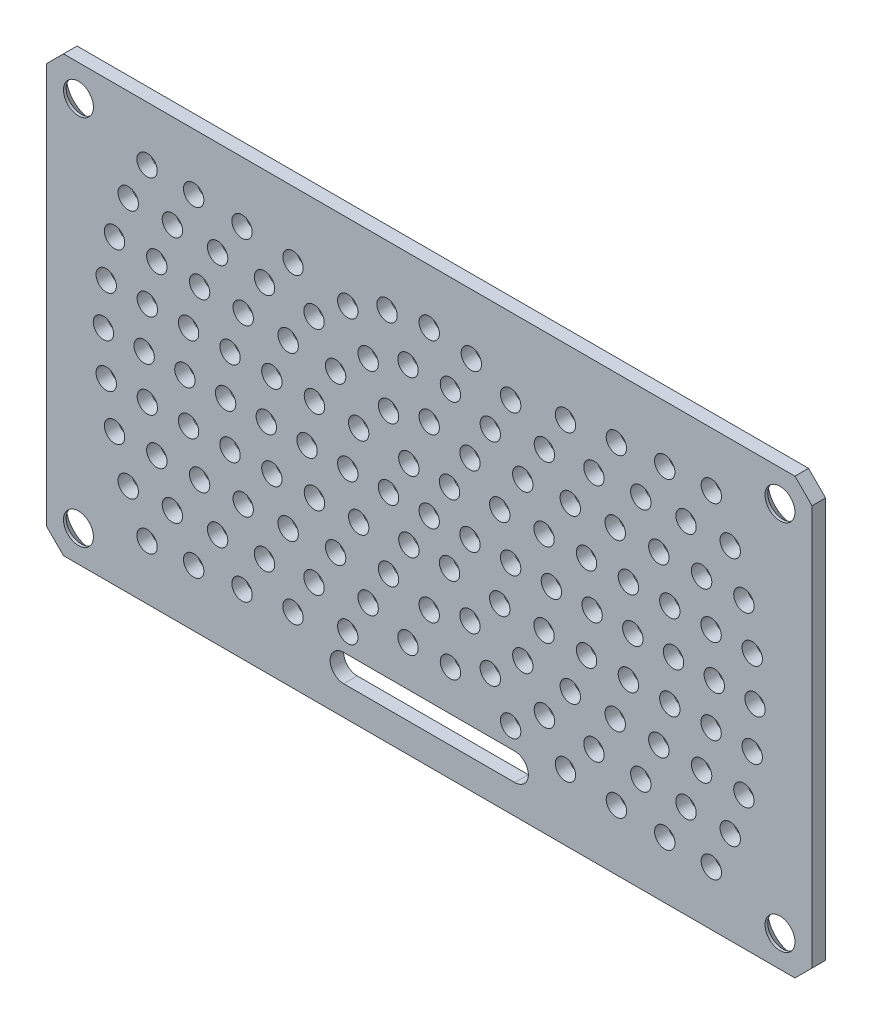
SolidWorks part; units mm, degrees
ref_plane "Front Plane" through (0, 0, 0) normal (0, 0, 1) x (1, 0, 0)
ref_plane "Top Plane" through (0, 0, 0) normal (0, 1, 0) x (1, 0, 0)
ref_plane "Right Plane" through (0, 0, 0) normal (1, 0, 0) x (0, 0, -1)
sketch "Sketch1" plane through (0, 0, 0) normal (0, 0, 1) x (1, 0, 0)
  line L1 (0, 0) -> (89.5, 0)
  line L2 (0, 0) -> (0, 50.8)
  line L3 (0, 50.8) -> (89.5, 50.8)
  line L4 (89.5, 0) -> (89.5, 50.8)
  dimension "D1" = 89.5
  dimension "D2" = 50.8
extrude "Boss-Extrude1" add sketch "Sketch1" along normal blind 1.5875
chamfer "Chamfer1" distance 2 angle 45 4 edges at (0, 0, 0.7937) (0, 50.8, 0.7937) (89.5, 0, 0.7937) (89.5, 50.8, 0.7937)
sketch "Sketch3" plane through (0, 0, 0) normal (0, 0, -1) x (-1, 0, 0)
  line L0 (-89.5, 25.4) -> (0, 25.4) construction
  line L1 (-89.5, 2) -> (-89.5, 48.8) construction
  line L2 (0, 48.8) -> (0, 2) construction
  line L3 (-85.75, 47.15) -> (-3.75, 47.15) construction
  line L4 (-87.5, 50.8) -> (-2, 50.8) construction
  line L5 (-44.75, 50.8) -> (-44.75, 0) construction
  line L6 (-2, 0) -> (-87.5, 0) construction
  line L7 (-3.75, 47.15) -> (-3.75, 3.65) construction
  circle A0 centre (-85.75, 47.15) radius 1.75
  circle A1 centre (-3.75, 47.15) radius 1.75
  circle A2 centre (-3.75, 3.65) radius 1.75
  circle A3 centre (-85.75, 3.65) radius 1.75
  point P20 (-44.75, 47.15)
  point P21 (-3.75, 25.4)
  dimension "D1" = 3.5
  dimension "D2" = 82
  dimension "D3" = 43.5
extrude "Cut-Extrude2" cut sketch "Sketch3" against normal through all
chamfer "Chamfer2" distance 1.27 angle 45 4 edges at (2, 3.65, 0) (84, 3.65, 0) (2, 47.15, 0) (84, 47.15, 0)
sketch "Sketch4" plane through (0, 0, 0) normal (0, 0, -1) x (-1, 0, 0)
  line L0 (-44.75, 50.8) -> (-44.75, 0) construction
  line L1 (-87.5, 50.8) -> (-2, 50.8) construction
  line L2 (-2, 0) -> (-87.5, 0) construction
  circle A0 centre (-44.75, 25.4) radius 1.1906
  circle A1 centre (-39.99, 25.4) radius 1.1906
  circle A2 centre (-35.23, 25.4) radius 1.1906
  circle A3 centre (-30.47, 25.4) radius 1.1906
  circle A4 centre (-25.71, 25.4) radius 1.1906
  circle A5 centre (-20.95, 25.4) radius 1.1906
  circle A6 centre (-16.19, 25.4) radius 1.1906
  circle A7 centre (-11.43, 25.4) radius 1.1906
  circle A8 centre (-6.67, 25.4) radius 1.1906
  circle A10 centre (-42.37, 21.2777) radius 1.1906
  circle A11 centre (-47.13, 21.2777) radius 1.1906
  circle A12 centre (-49.51, 25.4) radius 1.1906
  circle A13 centre (-47.13, 29.5223) radius 1.1906
  circle A14 centre (-42.37, 29.5223) radius 1.1906
  circle A15 centre (-36.5054, 20.64) radius 1.1906
  circle A16 centre (-39.99, 17.1554) radius 1.1906
  circle A17 centre (-44.75, 15.88) radius 1.1906
  circle A18 centre (-49.51, 17.1554) radius 1.1906
  circle A19 centre (-52.9946, 20.64) radius 1.1906
  circle A20 centre (-54.27, 25.4) radius 1.1906
  circle A21 centre (-52.9946, 30.16) radius 1.1906
  circle A22 centre (-49.51, 33.6446) radius 1.1906
  circle A23 centre (-44.75, 34.92) radius 1.1906
  circle A24 centre (-39.99, 33.6446) radius 1.1906
  circle A25 centre (-36.5054, 30.16) radius 1.1906
  circle A26 centre (-31.3312, 20.516) radius 1.1906
  circle A27 centre (-33.8109, 16.221) radius 1.1906
  circle A28 centre (-37.61, 13.0332) radius 1.1906
  circle A29 centre (-42.2703, 11.3369) radius 1.1906
  circle A30 centre (-47.2297, 11.3369) radius 1.1906
  circle A31 centre (-51.89, 13.0332) radius 1.1906
  circle A32 centre (-55.6891, 16.221) radius 1.1906
  circle A33 centre (-58.1688, 20.516) radius 1.1906
  circle A34 centre (-59.03, 25.4) radius 1.1906
  circle A35 centre (-58.1688, 30.284) radius 1.1906
  circle A36 centre (-55.6891, 34.579) radius 1.1906
  circle A37 centre (-51.89, 37.7668) radius 1.1906
  circle A38 centre (-47.2297, 39.4631) radius 1.1906
  circle A39 centre (-42.2703, 39.4631) radius 1.1906
  circle A40 centre (-37.61, 37.7668) radius 1.1906
  circle A41 centre (-33.8109, 34.579) radius 1.1906
  circle A42 centre (-31.3312, 30.284) radius 1.1906
  circle A43 centre (-26.3588, 20.4721) radius 1.1906
  circle A44 centre (-28.2609, 15.88) radius 1.1906
  circle A45 centre (-31.2867, 11.9367) radius 1.1906
  circle A46 centre (-35.23, 8.9109) radius 1.1906
  circle A50 centre (-54.27, 8.9109) radius 1.1906
  circle A51 centre (-58.2133, 11.9367) radius 1.1906
  circle A52 centre (-61.2391, 15.88) radius 1.1906
  circle A53 centre (-63.1412, 20.4721) radius 1.1906
  circle A54 centre (-63.79, 25.4) radius 1.1906
  circle A55 centre (-63.1412, 30.3279) radius 1.1906
  circle A56 centre (-61.2391, 34.92) radius 1.1906
  circle A57 centre (-58.2133, 38.8633) radius 1.1906
  circle A58 centre (-54.27, 41.8891) radius 1.1906
  circle A59 centre (-49.6779, 43.7912) radius 1.1906
  circle A60 centre (-44.75, 44.44) radius 1.1906
  circle A61 centre (-39.8221, 43.7912) radius 1.1906
  circle A62 centre (-35.23, 41.8891) radius 1.1906
  circle A63 centre (-31.2867, 38.8633) radius 1.1906
  circle A64 centre (-28.2609, 34.92) radius 1.1906
  circle A65 centre (-26.3588, 30.3279) radius 1.1906
  circle A66 centre (-21.4701, 20.4517) radius 1.1906
  circle A67 centre (-23.0076, 15.7197) radius 1.1906
  circle A68 centre (-25.4954, 11.4107) radius 1.1906
  circle A69 centre (-28.8247, 7.7132) radius 1.1906
  circle A76 centre (-60.6753, 7.7132) radius 1.1906
  circle A77 centre (-64.0046, 11.4107) radius 1.1906
  circle A78 centre (-66.4924, 15.7197) radius 1.1906
  circle A79 centre (-68.0299, 20.4517) radius 1.1906
  circle A80 centre (-68.55, 25.4) radius 1.1906
  circle A81 centre (-68.0299, 30.3483) radius 1.1906
  circle A82 centre (-66.4924, 35.0803) radius 1.1906
  circle A83 centre (-64.0046, 39.3893) radius 1.1906
  circle A84 centre (-60.6753, 43.0868) radius 1.1906
  circle A91 centre (-28.8247, 43.0868) radius 1.1906
  circle A92 centre (-25.4954, 39.3893) radius 1.1906
  circle A93 centre (-23.0076, 35.0803) radius 1.1906
  circle A94 centre (-21.4701, 30.3483) radius 1.1906
  circle A95 centre (-16.6239, 20.4406) radius 1.1906
  circle A96 centre (-17.9124, 15.6319) radius 1.1906
  circle A97 centre (-20.0163, 11.12) radius 1.1906
  circle A98 centre (-22.8718, 7.042) radius 1.1906
  circle A108 centre (-66.6282, 7.042) radius 1.1906
  circle A109 centre (-69.4837, 11.12) radius 1.1906
  circle A110 centre (-71.5876, 15.6319) radius 1.1906
  circle A111 centre (-72.8761, 20.4406) radius 1.1906
  circle A112 centre (-73.31, 25.4) radius 1.1906
  circle A113 centre (-72.8761, 30.3594) radius 1.1906
  circle A114 centre (-71.5876, 35.1681) radius 1.1906
  circle A115 centre (-69.4837, 39.68) radius 1.1906
  circle A116 centre (-66.6282, 43.758) radius 1.1906
  circle A126 centre (-22.8718, 43.758) radius 1.1906
  circle A127 centre (-20.0163, 39.68) radius 1.1906
  circle A128 centre (-17.9124, 35.1681) radius 1.1906
  circle A129 centre (-16.6239, 30.3594) radius 1.1906
  circle A130 centre (-11.8022, 20.4339) radius 1.1906
  circle A131 centre (-12.9103, 15.5788) radius 1.1906
  circle A132 centre (-14.7297, 10.943) radius 1.1906
  circle A133 centre (-17.2197, 6.6302) radius 1.1906
  circle A146 centre (-72.2803, 6.6302) radius 1.1906
  circle A147 centre (-74.7703, 10.943) radius 1.1906
  circle A148 centre (-76.5897, 15.5788) radius 1.1906
  circle A149 centre (-77.6978, 20.4339) radius 1.1906
  circle A150 centre (-78.07, 25.4) radius 1.1906
  circle A151 centre (-77.6978, 30.3661) radius 1.1906
  circle A152 centre (-76.5897, 35.2212) radius 1.1906
  circle A153 centre (-74.7703, 39.857) radius 1.1906
  circle A154 centre (-72.2803, 44.1698) radius 1.1906
  circle A167 centre (-17.2197, 44.1698) radius 1.1906
  circle A168 centre (-14.7297, 39.857) radius 1.1906
  circle A169 centre (-12.9103, 35.2212) radius 1.1906
  circle A170 centre (-11.8022, 30.3661) radius 1.1906
  circle A171 centre (-6.9958, 20.4296) radius 1.1906
  circle A172 centre (-7.9675, 15.5442) radius 1.1906
  circle A173 centre (-9.5687, 10.8274) radius 1.1906
  circle A174 centre (-11.7718, 6.36) radius 1.1906
  circle A190 centre (-77.7282, 6.36) radius 1.1906
  circle A191 centre (-79.9313, 10.8274) radius 1.1906
  circle A192 centre (-81.5325, 15.5442) radius 1.1906
  circle A193 centre (-82.5042, 20.4296) radius 1.1906
  circle A194 centre (-82.83, 25.4) radius 1.1906
  circle A195 centre (-82.5042, 30.3704) radius 1.1906
  circle A196 centre (-81.5325, 35.2558) radius 1.1906
  circle A197 centre (-79.9313, 39.9726) radius 1.1906
  circle A198 centre (-77.7282, 44.44) radius 1.1906
  circle A214 centre (-11.7718, 44.44) radius 1.1906
  circle A215 centre (-9.5687, 39.9726) radius 1.1906
  circle A216 centre (-7.9675, 35.2558) radius 1.1906
  circle A217 centre (-6.9958, 30.3704) radius 1.1906
  circle A271 centre (-49.7094, 53.5261) radius 1.1906 [skipped]
  circle A272 centre (-44.75, 53.96) radius 1.1906 [skipped]
  circle A273 centre (-39.7906, 53.5261) radius 1.1906 [skipped]
  circle A274 centre (-61.41, 54.256) radius 1.1906 [skipped]
  circle A275 centre (-56.9232, 56.4167) radius 1.1906 [skipped]
  circle A276 centre (-52.1644, 57.8846) radius 1.1906 [skipped]
  circle A277 centre (-47.24, 58.6268) radius 1.1906 [skipped]
  circle A278 centre (-42.26, 58.6268) radius 1.1906 [skipped]
  circle A279 centre (-37.3356, 57.8846) radius 1.1906 [skipped]
  circle A280 centre (-32.5768, 56.4167) radius 1.1906 [skipped]
  circle A281 centre (-28.09, 54.256) radius 1.1906 [skipped]
  circle A282 centre (-71.6766, 52.3266) radius 1.1906 [skipped]
  circle A283 centre (-67.9316, 55.6109) radius 1.1906 [skipped]
  circle A284 centre (-63.79, 58.3782) radius 1.1906 [skipped]
  circle A285 centre (-59.3226, 60.5813) radius 1.1906 [skipped]
  circle A286 centre (-54.6058, 62.1825) radius 1.1906 [skipped]
  circle A287 centre (-49.7204, 63.1542) radius 1.1906 [skipped]
  circle A288 centre (-44.75, 63.48) radius 1.1906 [skipped]
  circle A289 centre (-39.7796, 63.1542) radius 1.1906 [skipped]
  circle A290 centre (-34.8942, 62.1825) radius 1.1906 [skipped]
  circle A291 centre (-30.1774, 60.5813) radius 1.1906 [skipped]
  circle A292 centre (-25.71, 58.3782) radius 1.1906 [skipped]
  circle A293 centre (-21.5684, 55.6109) radius 1.1906 [skipped]
  circle A309 centre (-59.03, 50.1337) radius 1.1906 [skipped]
  circle A310 centre (-54.5181, 52.2376) radius 1.1906 [skipped]
  circle A311 centre (-65.5247, 51.4506) radius 1.1906 [skipped]
  circle A312 centre (-23.9753, 51.4506) radius 1.1906 [skipped]
  circle A313 centre (-17.8234, 52.3266) radius 1.1906 [skipped]
  circle A315 centre (-34.9819, 52.2376) radius 1.1906 [skipped]
  circle A316 centre (-30.47, 50.1337) radius 1.1906 [skipped]
  circle A319 centre (-34.9819, -1.4376) radius 1.1906 [skipped]
  circle A320 centre (-39.7906, -2.7261) radius 1.1906 [skipped]
  circle A321 centre (-44.75, -3.16) radius 1.1906 [skipped]
  circle A322 centre (-49.7094, -2.7261) radius 1.1906 [skipped]
  circle A323 centre (-54.5181, -1.4376) radius 1.1906 [skipped]
  circle A324 centre (-23.9753, -0.6506) radius 1.1906 [skipped]
  circle A325 centre (-28.09, -3.456) radius 1.1906 [skipped]
  circle A326 centre (-32.5768, -5.6167) radius 1.1906 [skipped]
  circle A327 centre (-37.3356, -7.0846) radius 1.1906 [skipped]
  circle A328 centre (-42.26, -7.8268) radius 1.1906 [skipped]
  circle A329 centre (-47.24, -7.8268) radius 1.1906 [skipped]
  circle A330 centre (-52.1644, -7.0846) radius 1.1906 [skipped]
  circle A331 centre (-56.9232, -5.6167) radius 1.1906 [skipped]
  circle A332 centre (-61.41, -3.456) radius 1.1906 [skipped]
  circle A333 centre (-65.5247, -0.6506) radius 1.1906 [skipped]
  circle A334 centre (-17.8234, -1.5266) radius 1.1906 [skipped]
  circle A335 centre (-21.5684, -4.8109) radius 1.1906 [skipped]
  circle A336 centre (-25.71, -7.5782) radius 1.1906 [skipped]
  circle A337 centre (-30.1774, -9.7813) radius 1.1906 [skipped]
  circle A338 centre (-34.8942, -11.3825) radius 1.1906 [skipped]
  circle A339 centre (-39.7796, -12.3542) radius 1.1906 [skipped]
  circle A340 centre (-44.75, -12.68) radius 1.1906 [skipped]
  circle A341 centre (-49.7204, -12.3542) radius 1.1906 [skipped]
  circle A342 centre (-54.6058, -11.3825) radius 1.1906 [skipped]
  circle A343 centre (-59.3226, -9.7813) radius 1.1906 [skipped]
  circle A344 centre (-63.79, -7.5782) radius 1.1906 [skipped]
  circle A345 centre (-67.9316, -4.8109) radius 1.1906 [skipped]
  circle A346 centre (-71.6766, -1.5266) radius 1.1906 [skipped]
  circle A363 centre (-59.03, 0.6663) radius 1.1906 [skipped]
  circle A364 centre (-30.47, 0.6663) radius 1.1906 [skipped]
  circle A367 centre (-42.2622, 1.7304) radius 1.1906 [skipped]
  circle A368 centre (-47.2378, 1.7304) radius 1.1906 [skipped]
  circle A369 centre (-47.2378, 49.0696) radius 1.1906 [skipped]
  circle A370 centre (-42.2622, 49.0696) radius 1.1906 [skipped]
  circle A371 centre (-52.1046, 48.0351) radius 1.1906 [skipped]
  circle A372 centre (-37.3954, 48.0351) radius 1.1906 [skipped]
  circle A373 centre (-37.3954, 2.7649) radius 1.1906 [skipped]
  circle A374 centre (-52.1046, 2.7649) radius 1.1906 [skipped]
  circle A383 centre (-1.91, 25.4) radius 1.1906 [skipped]
  circle A384 centre (-74.9609, 48.5816) radius 1.1906 [skipped]
  circle A385 centre (-69.1753, 48.0634) radius 1.1906 [skipped]
  circle A386 centre (-63.108, 47.2782) radius 1.1906 [skipped]
  circle A387 centre (-14.5391, 48.5816) radius 1.1906 [skipped]
  circle A388 centre (-20.3247, 48.0634) radius 1.1906 [skipped]
  circle A389 centre (-26.392, 47.2782) radius 1.1906 [skipped]
  circle A390 centre (-74.9609, 2.2184) radius 1.1906 [skipped]
  circle A391 centre (-69.1753, 2.7366) radius 1.1906 [skipped]
  circle A392 centre (-63.108, 3.5218) radius 1.1906 [skipped]
  circle A393 centre (-26.392, 3.5218) radius 1.1906 [skipped]
  circle A394 centre (-20.3247, 2.7366) radius 1.1906 [skipped]
  circle A395 centre (-14.5391, 2.2184) radius 1.1906 [skipped]
  circle A396 centre (-56.65, 46.0114) radius 1.1906 [skipped]
  circle A397 centre (-32.85, 46.0114) radius 1.1906 [skipped]
  circle A398 centre (-32.85, 4.7886) radius 1.1906 [skipped]
  circle A399 centre (-56.65, 4.7886) radius 1.1906 [skipped]
  circle A400 centre (-39.8221, 7.0088) radius 1.1906 [skipped]
  circle A401 centre (-44.75, 6.36) radius 1.1906 [skipped]
  circle A402 centre (-49.6779, 7.0088) radius 1.1906 [skipped]
  point P38 (-44.75, 25.4)
  point P61 (-44.75, 25.4)
  point P96 (-44.75, 25.4)
  point P143 (-44.75, 25.4)
  point P202 (-44.75, 25.4)
  point P273 (-44.75, 25.4)
  point P357 (-44.75, 25.4)
  point P451 (-44.75, 25.4)
  point P558 (-44.75, 25.4)
  dimension "D1" = 2.3813
  dimension "D2" = 10
  dimension "D3" = 6
  dimension "D4" = 12
  dimension "D5" = 18
  dimension "D6" = 24
  dimension "D7" = 30
  dimension "D8" = 36
  dimension "D9" = 42
  dimension "D10" = 48
extrude "Cut-Extrude3" cut sketch "Sketch4" against normal through all
sketch "Sketch5" plane through (0, 0, 0) normal (0, 0, -1) x (-1, 0, 0)
  line L0 (-54.75, 5) -> (-34.75, 5) construction
  line L1 (-54.75, 6.5875) -> (-34.75, 6.5875)
  line L2 (-54.75, 3.4125) -> (-34.75, 3.4125)
  line L3 (-44.75, 0) -> (-44.75, 5) construction
  line L4 (-2, 0) -> (-87.5, 0) construction
  arc A0 (-54.75, 6.5875) -> (-54.75, 3.4125) centre (-54.75, 5) ccw
  arc A1 (-34.75, 3.4125) -> (-34.75, 6.5875) centre (-34.75, 5) ccw
  point P2 (-44.75, 5)
  dimension "D1" = 1.5875
  dimension "D2" = 20
  dimension "D3" = 5
extrude "Cut-Extrude4" cut sketch "Sketch5" against normal through all
